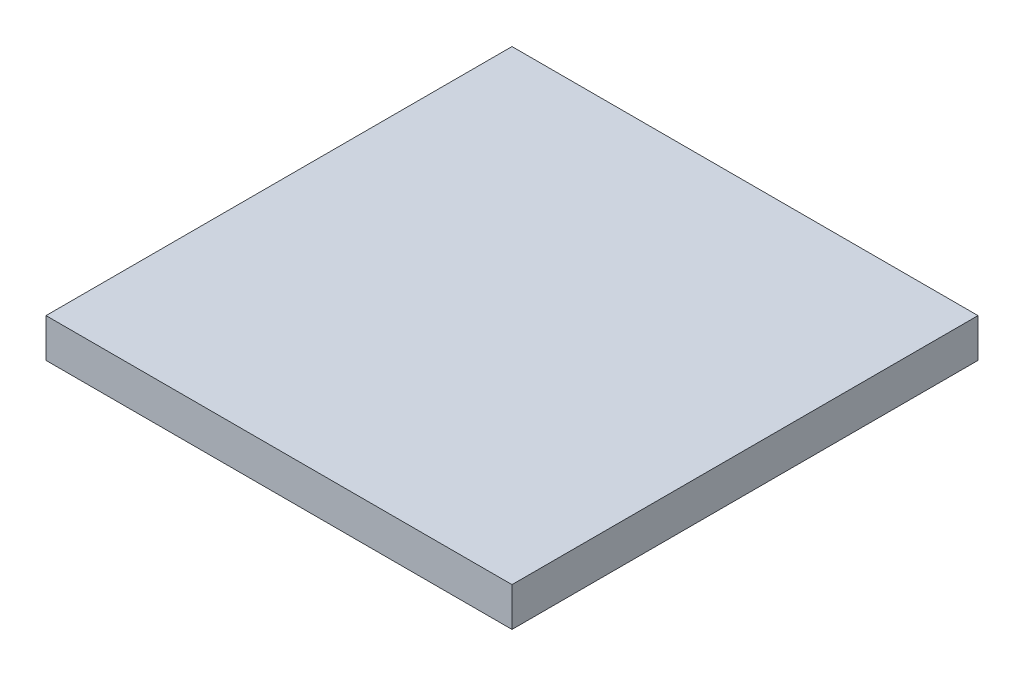
SolidWorks part; units mm, degrees
ref_plane "Спереди" through (0, 0, 0) normal (0, 0, 1) x (1, 0, 0)
ref_plane "Сверху" through (0, 0, 0) normal (0, 1, 0) x (1, 0, 0)
ref_plane "Справа" through (0, 0, 0) normal (1, 0, 0) x (0, 0, -1)
other "Configuration Table"
sketch "Эскиз1" plane through (0, 0, 0) normal (0, 1, 0) x (1, 0, 0)
  line L1 (0, 0) -> (12, 0)
  line L2 (0, 0) -> (0, 12)
  line L3 (0, 12) -> (12, 12)
  line L4 (12, 0) -> (12, 12)
extrude "Бобышка-Вытянуть1" add sketch "Эскиз1" along normal blind 1
